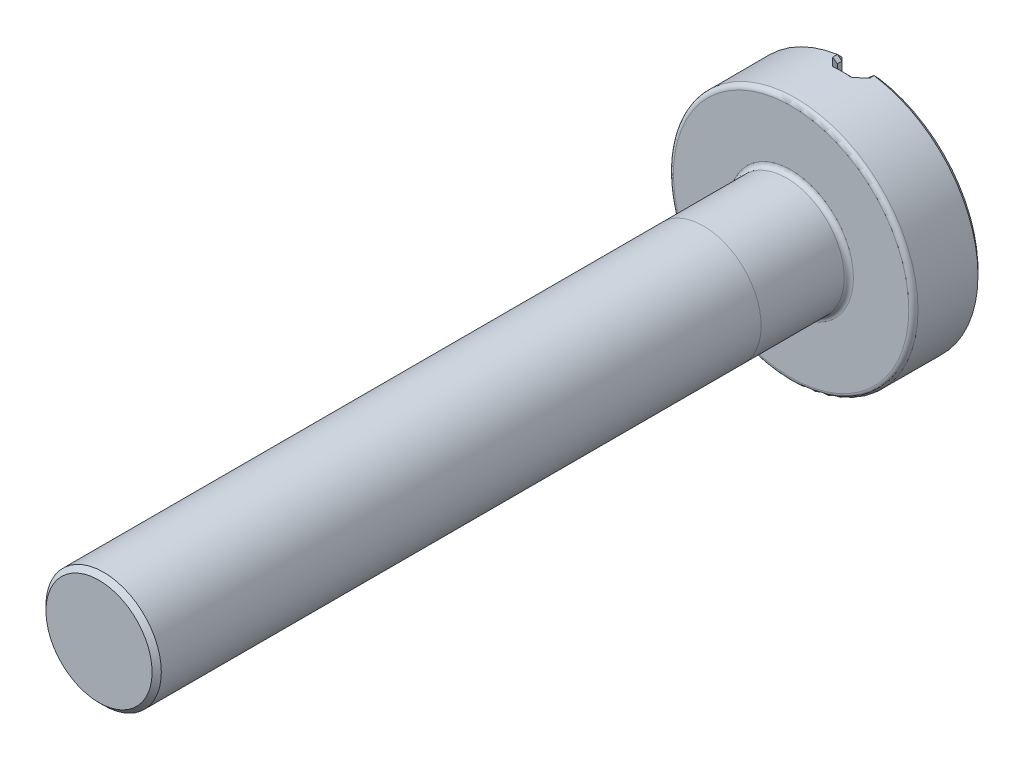
SolidWorks part; units mm, degrees
ref_plane "Front Plane" through (0, 0, 0) normal (0, 0, 1) x (1, 0, 0)
ref_plane "Top Plane" through (0, 0, 0) normal (0, 1, 0) x (1, 0, 0)
ref_plane "Right Plane" through (0, 0, 0) normal (1, 0, 0) x (0, 0, -1)
sketch "Sketch1" plane through (0, 0, 0) normal (0, 0, 1) x (1, 0, 0)
  circle A0 centre (0, 0) radius 0.625
  dimension "D1" = 1.25
extrude "Boss-Extrude1" add sketch "Sketch1" along normal blind 7.5
sketch "Sketch2" plane through (0, 0, 0) normal (0, 0, 1) x (1, 0, 0)
  circle A2 centre (0, 0) radius 1.325
  circle A3 centre (0, 0) radius 1.325
  dimension "D1" = 0.7
extrude "Boss-Extrude2" add sketch "Sketch2" against normal blind 0.75
sketch "Sketch3" plane through (0, 0, -0.75) normal (0, 0, -1) x (-1, 0, 0)
  line L1 (0.15, -3.841) -> (-0.15, -3.841)
  line L2 (0.15, -3.841) -> (0.15, 3.841)
  line L3 (0.15, 3.841) -> (-0.15, 3.841)
  line L4 (-0.15, -3.841) -> (-0.15, 3.841)
  line L5 (0.15, -3.841) -> (-0.15, 3.841) construction
  line L6 (0.15, 3.841) -> (-0.15, -3.841) construction
  point P0 (0, 0)
  dimension "D1" = 0.3
extrude "Cut-Extrude1" cut sketch "Sketch3" against normal blind 0.15
chamfer "Chamfer1" distance 0.05 angle 45 12 edges at (-0.15, 0, -0.75) (-1.325, 0, -0.75) (0.15, 0, -0.75) (1.325, 0, -0.75) (0.15, 0, -0.6) (-0.15, 0, -0.6) (-0.15, -1.3165, -0.675) (-0.15, 1.3165, -0.675) (0.15, 1.3165, -0.675) (0.15, -1.3165, -0.675) (0, 1.325, -0.6) (0, -1.325, -0.6)
fillet "Fillet1" radius 0.05 2 edges at (1.325, 0, 0) (0.625, 0, 0)
chamfer "Chamfer2" distance 0.05 angle 45 1 edges at (0.625, 0, 7.5)
sketch "Sketch5" plane through (0, 0, 0) normal (1, 0, 0) x (0, 0, -1)
  line L0 (-0.95, 3.1714) -> (-0.95, -2.5701)
  line L1 (-7.45, -0.625) -> (-7.45, 0.625) construction
  dimension "D1" = 6.5
split line "Split Line3"
